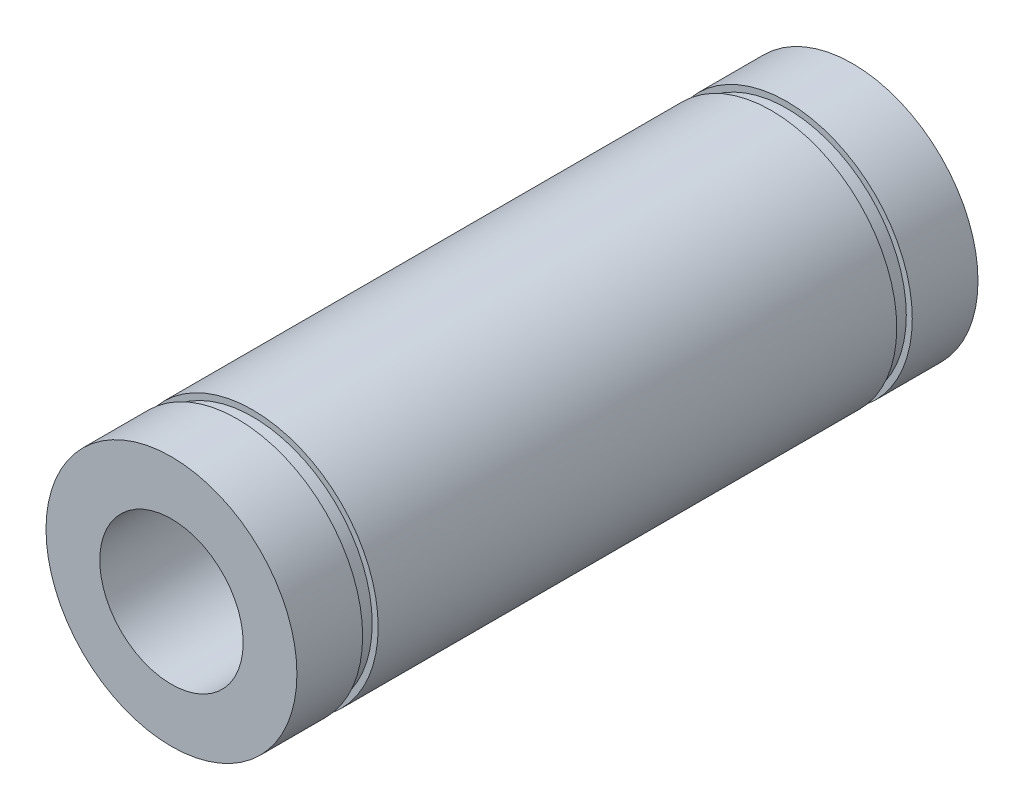
SolidWorks part; units mm, degrees
ref_plane "Front Plane" through (0, 0, 0) normal (0, 0, 1) x (1, 0, 0)
ref_plane "Top Plane" through (0, 0, 0) normal (0, 1, 0) x (1, 0, 0)
ref_plane "Right Plane" through (0, 0, 0) normal (1, 0, 0) x (0, 0, -1)
sketch "Sketch1" plane through (0, 0, 0) normal (0, 1, 0) x (1, 0, 0)
  line L0 (10.5, 22) -> (6, 22)
  line L1 (6, 22) -> (6, -35)
  line L2 (6, -35) -> (10.5, -35)
  line L3 (10.5, -35) -> (10.5, -29.5)
  line L4 (10.5, -29.5) -> (10, -29.5)
  line L5 (10, -29.5) -> (10, -28.2)
  line L6 (10, -28.2) -> (10.5, -28.2)
  line L7 (10.5, -28.2) -> (10.5, 15.2)
  line L8 (10.5, 15.2) -> (10, 15.2)
  line L9 (10, 15.2) -> (10, 16.5)
  line L10 (10, 16.5) -> (10.5, 16.5)
  line L11 (10.5, 16.5) -> (10.5, 22)
  line L12 (0, 0) -> (0, -30) construction
  dimension "D1" = 12
  dimension "D2" = 21
  dimension "D3" = 57
  dimension "D4" = 46
  dimension "D5" = 1.3
revolve "Revolve1" add sketch "Sketch1" angle 360 about L12
